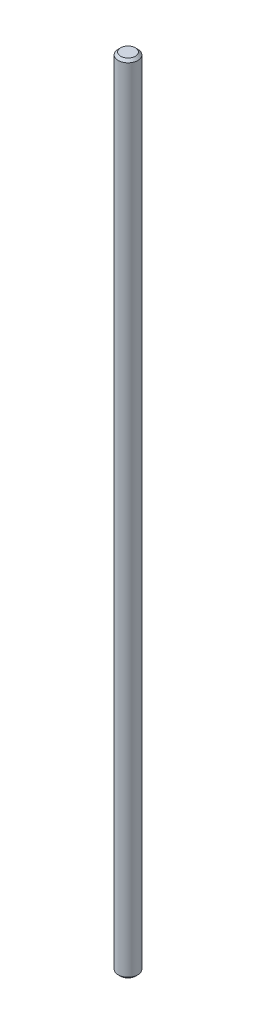
SolidWorks part; units mm, degrees
material "Chrome Stainless Steel"
ref_plane "Front Plane" through (0, 0, 0) normal (0, 0, 1) x (1, 0, 0)
ref_plane "Top Plane" through (0, 0, 0) normal (0, 1, 0) x (1, 0, 0)
ref_plane "Right Plane" through (0, 0, 0) normal (1, 0, 0) x (0, 0, -1)
sketch "Sketch1" plane through (0, 0, 0) normal (1, 0, 0) x (0, 0, -1)
  line L0 (0, 0) -> (0, 325)
  line L1 (0, 0) -> (3.0724, 0)
  line L2 (3.0724, 0) -> (4, 0.9276)
  line L3 (4, 0.9276) -> (4, 324)
  line L4 (4, 324) -> (3, 325)
  line L5 (3, 325) -> (0, 325)
  line L6 (0, -514.8816) -> (0, 25229.2008) construction
  point P4 (0, 0)
  dimension "D1" = 8
  dimension "D2" = 1
  dimension "D3" = 1
  dimension "D4" = 325
revolve "Revolve1" add sketch "Sketch1" angle 360 about L6
